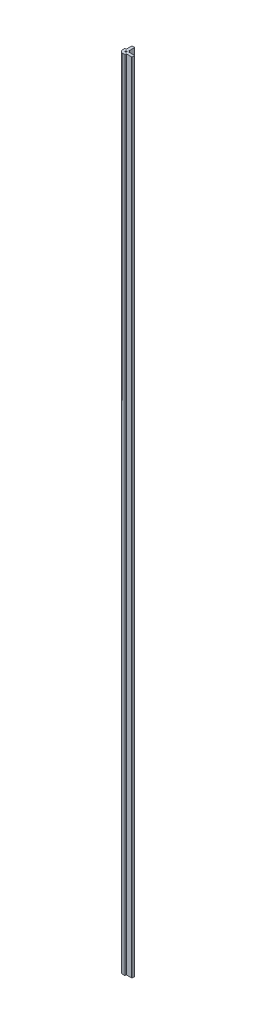
SolidWorks part; units mm, degrees
material "6063-T6"
ref_plane "Front" through (0, 0, 0) normal (0, 0, 1) x (1, 0, 0)
ref_plane "Top" through (0, 0, 0) normal (0, 1, 0) x (1, 0, 0)
ref_plane "Right" through (0, 0, 0) normal (1, 0, 0) x (0, 0, -1)
sketch "Sketch1" plane through (0, 0, 0) normal (0, 1, 0) x (1, 0, 0)
  line L0 (-4.445, 17.018) -> (-4.445, 4.953)
  line L1 (0, -7.62) -> (4.572, -7.62)
  line L2 (-7.62, 0) -> (-7.62, 4.572)
  line L3 (-3.683, 17.78) -> (1.143, 17.78)
  line L4 (17.78, -3.683) -> (17.78, 1.143)
  line L5 (17.018, -4.445) -> (4.953, -4.445)
  line L6 (4.826, -4.572) -> (4.826, -7.366)
  line L7 (-4.572, 4.826) -> (-7.366, 4.826)
  line L9 (1.905, 17.018) -> (1.905, 4.8775)
  line L10 (4.8775, 1.905) -> (17.018, 1.905)
  arc A0 (0, -7.62) -> (-7.62, 0) centre (0, 0) cw
  arc A1 (4.953, -4.445) -> (4.826, -4.572) centre (4.953, -4.572) ccw
  arc A2 (-4.445, 4.953) -> (-4.572, 4.826) centre (-4.572, 4.953) cw
  arc A7 (17.018, -4.445) -> (17.78, -3.683) centre (17.018, -3.683) ccw
  arc A8 (-4.445, 17.018) -> (-3.683, 17.78) centre (-3.683, 17.018) cw
  arc A9 (4.826, -7.366) -> (4.572, -7.62) centre (4.572, -7.366) cw
  arc A10 (-7.366, 4.826) -> (-7.62, 4.572) centre (-7.366, 4.572) ccw
  arc A11 (4.6453, 2.0562) -> (2.0562, 4.6453) centre (0, 0) ccw
  arc A12 (1.905, 17.018) -> (1.143, 17.78) centre (1.143, 17.018) ccw
  arc A13 (17.018, 1.905) -> (17.78, 1.143) centre (17.018, 1.143) cw
  arc A14 (2.0562, 4.6453) -> (1.905, 4.8775) centre (2.159, 4.8775) cw
  arc A15 (4.6453, 2.0562) -> (4.8775, 1.905) centre (4.8775, 2.159) ccw
  point P0 (0, 0)
  point P20 (-4.445, 4.826)
  point P28 (-7.62, 4.826)
  point P35 (-4.445, 17.78)
  dimension "D3" = 7.62
  dimension "D8" = 0.127
  dimension "D10" = 0.254
  dimension "D4" = 5.08
  dimension "D5" = 0.762
  dimension "D2" = 25.4
  dimension "D6" = 3.175
  dimension "D7" = 12.954
  dimension "D11" = 9.525
extrude "Boss-Extrude1" add sketch "Sketch1" along normal blind 1828.8
hole_wizard "THRU HOLES" positions "Sketch2" profile "Sketch3" hole size "#6-32" standard "ANSI Inch" end condition through all
sketch "Sketch2" plane through (0, 1828.8, 0) normal (0, 1, 0) x (1, 0, 0)
  point P0 (0, 0)
sketch "Sketch3" plane through (0, 1828.8, 0) normal (1, 0, 0) x (0, 0, 1)
  line L0 (0, 0) -> (0, 1828.8)
  line L1 (0, 1828.8) -> (1.7272, 1828.8)
  line L2 (1.7272, 1828.8) -> (1.7272, 0)
  line L5 (1.7272, 0) -> (0, 0)
  line L11 (0, -6.35) -> (0, 107.95) construction
  dimension "Thru Hole Dia." = 3.4544
  dimension "Thru Hole Depth" = 1828.8
